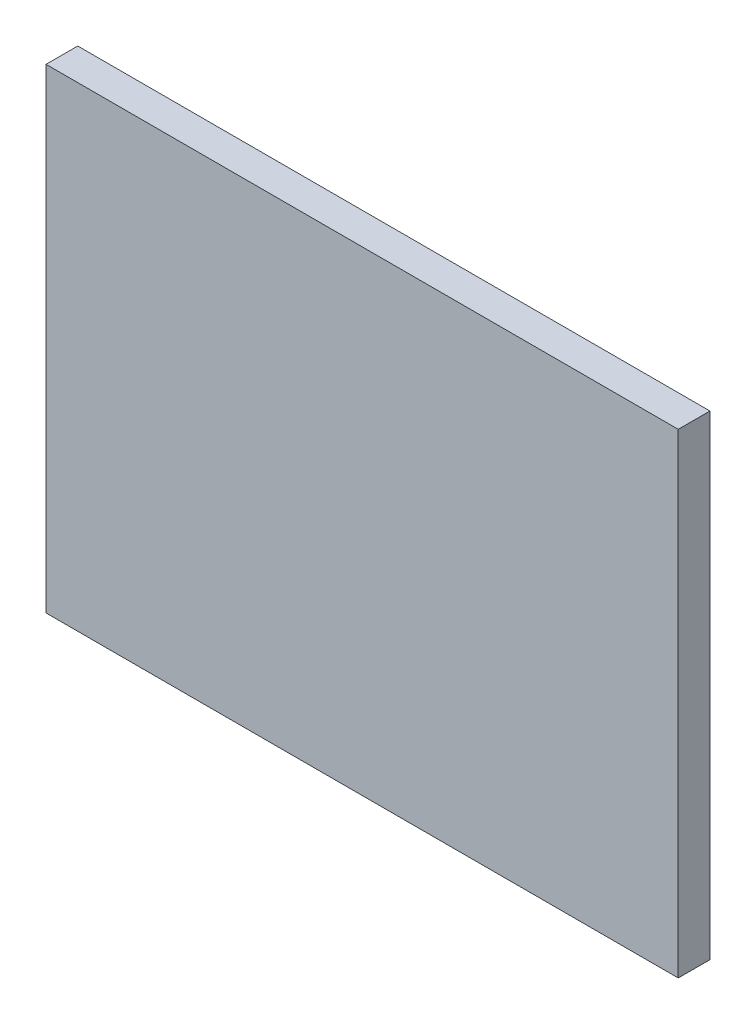
SolidWorks part; units mm, degrees
ref_plane "Plan de face" through (0, 0, 0) normal (0, 0, 1) x (1, 0, 0)
ref_plane "Plan de dessus" through (0, 0, 0) normal (0, 1, 0) x (1, 0, 0)
ref_plane "Plan de droite" through (0, 0, 0) normal (1, 0, 0) x (0, 0, -1)
sketch "Esquisse1" plane through (0, 0, 0) normal (0, 0, 1) x (1, 0, 0)
  line L1 (0, 0) -> (117.65, 0)
  line L2 (0, 0) -> (0, 88.43)
  line L3 (0, 88.43) -> (117.65, 88.43)
  line L4 (117.65, 0) -> (117.65, 88.43)
  dimension "D1" = 88.43
  dimension "D2" = 117.65
extrude "Boss.-Extru.1" add sketch "Esquisse1" along normal blind 5.9
